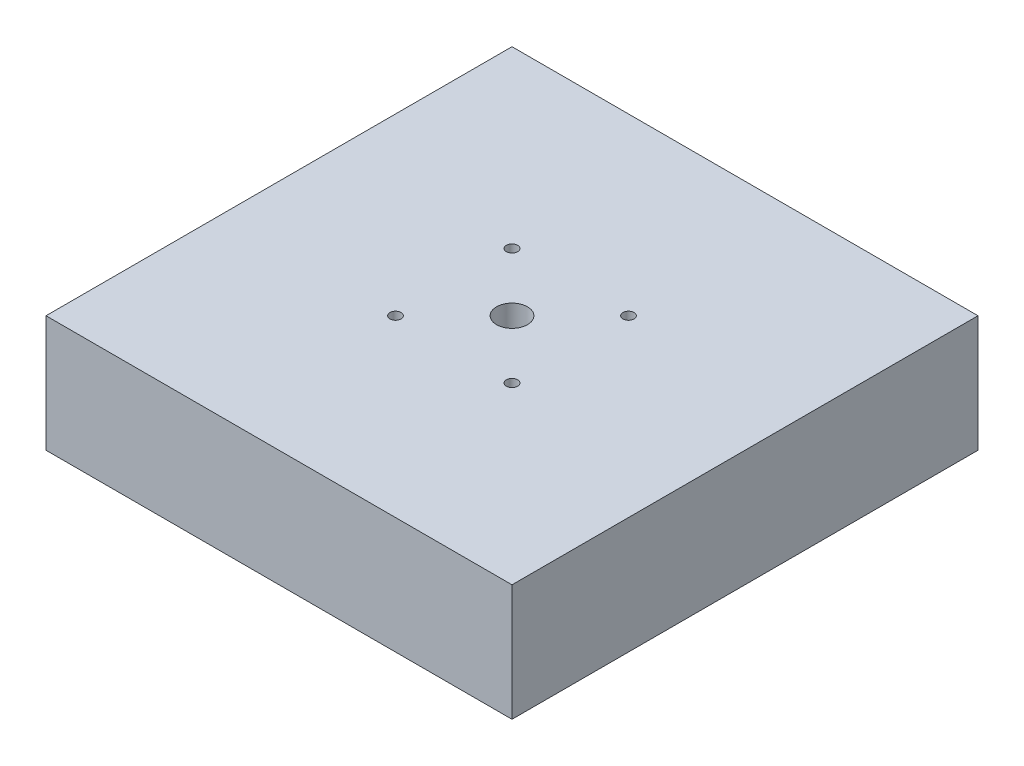
SolidWorks part; units mm, degrees
ref_plane "Front Plane" through (0, 0, 0) normal (0, 0, 1) x (1, 0, 0)
ref_plane "Top Plane" through (0, 0, 0) normal (0, 1, 0) x (1, 0, 0)
ref_plane "Right Plane" through (0, 0, 0) normal (1, 0, 0) x (0, 0, -1)
sketch "Sketch1" plane through (0, 0, 0) normal (0, 1, 0) x (1, 0, 0)
  line L1 (50.8, 50.8) -> (-50.8, 50.8)
  line L2 (50.8, 50.8) -> (50.8, -50.8)
  line L3 (50.8, -50.8) -> (-50.8, -50.8)
  line L4 (-50.8, 50.8) -> (-50.8, -50.8)
  line L5 (50.8, 50.8) -> (-50.8, -50.8) construction
  line L6 (50.8, -50.8) -> (-50.8, 50.8) construction
  point P0 (0, 0)
  dimension "D1" = 101.6
extrude "Boss-Extrude1" add sketch "Sketch1" along normal blind 25.4
hole_wizard "1/4 Clearance Hole1" positions "Sketch2" profile "Sketch3" hole size "1/4" standard "ANSI Inch" end condition through all
sketch "Sketch2" plane through (0, 25.4, 0) normal (0, 1, 0) x (1, 0, 0)
  point P0 (0, 0)
sketch "Sketch3" plane through (0, 25.4, 0) normal (1, 0, 0) x (0, 0, 1)
  line L0 (0, 0) -> (0, 25.4)
  line L1 (0, 25.4) -> (3.3782, 25.4)
  line L2 (3.3782, 25.4) -> (3.3782, 0)
  line L3 (3.3782, 0) -> (0, 0)
  line L4 (0, -6.35) -> (0, 107.95) construction
  dimension "Thru Hole Dia." = 6.7564
  dimension "Thru Hole Depth" = 25.4
hole_wizard "#2 Clearance Hole1" positions "Sketch4" profile "Sketch5" hole size "#2" standard "ANSI Inch" end condition through all
sketch "Sketch4" plane through (0, 25.4, 0) normal (0, 1, 0) x (1, 0, 0)
  line L1 (12.7, -12.7) -> (-12.7, -12.7)
  line L2 (12.7, -12.7) -> (12.7, 12.7)
  line L3 (12.7, 12.7) -> (-12.7, 12.7)
  line L4 (-12.7, -12.7) -> (-12.7, 12.7)
  line L5 (12.7, -12.7) -> (-12.7, 12.7) construction
  line L6 (12.7, 12.7) -> (-12.7, -12.7) construction
  point P0 (-12.7, 12.7)
  point P3 (0, 0)
sketch "Sketch5" plane through (-12.7, 25.4, -12.7) normal (1, 0, 0) x (0, 0, 1)
  line L0 (0, 0) -> (0, 25.4)
  line L1 (0, 25.4) -> (1.2192, 25.4)
  line L2 (1.2192, 25.4) -> (1.2192, 0)
  line L3 (1.2192, 0) -> (0, 0)
  line L4 (0, -6.35) -> (0, 107.95) construction
  dimension "Thru Hole Dia." = 2.4384
  dimension "Thru Hole Depth" = 25.4
hole_wizard "#2 Clearance Hole2" positions "Sketch6" profile "Sketch7" hole size "#2" standard "ANSI Inch" end condition through all
sketch "Sketch6" plane through (0, 25.4, 0) normal (0, 1, 0) x (1, 0, 0)
  point P0 (12.7, 12.7)
  point P1 (-12.7, -12.7)
  point P2 (12.7, -12.7)
sketch "Sketch7" plane through (12.7, 25.4, -12.7) normal (1, 0, 0) x (0, 0, 1)
  line L0 (0, 0) -> (0, 25.4)
  line L1 (0, 25.4) -> (1.2192, 25.4)
  line L2 (1.2192, 25.4) -> (1.2192, 0)
  line L3 (1.2192, 0) -> (0, 0)
  line L4 (0, -6.35) -> (0, 107.95) construction
  dimension "Thru Hole Dia." = 2.4384
  dimension "Thru Hole Depth" = 25.4
